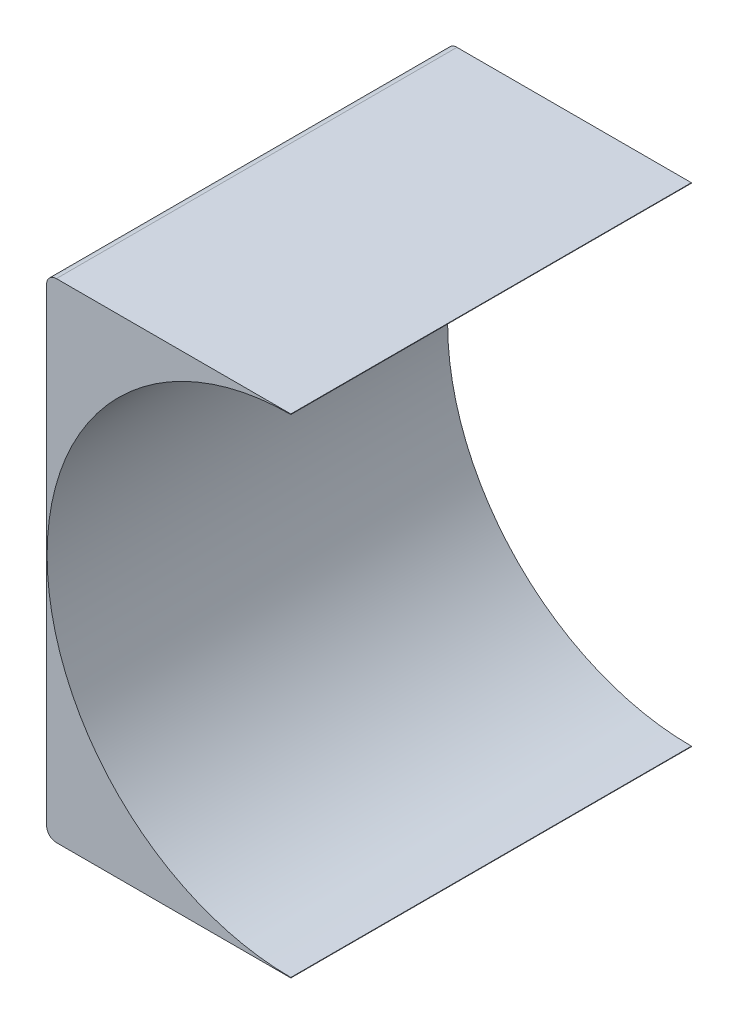
SolidWorks part; units mm, degrees
ref_plane "Спереди" through (0, 0, 0) normal (0, 0, 1) x (1, 0, 0)
ref_plane "Сверху" through (0, 0, 0) normal (0, 1, 0) x (1, 0, 0)
ref_plane "Справа" through (0, 0, 0) normal (1, 0, 0) x (0, 0, -1)
other "Configuration Table"
sketch "Эскиз1" plane through (0, 0, 0) normal (0, 1, 0) x (1, 0, 0)
  line L1 (12.5, -20.5) -> (-12.5, -20.5)
  line L2 (12.5, -20.5) -> (12.5, 20.5)
  line L3 (12.5, 20.5) -> (-12.5, 20.5)
  line L4 (-12.5, -20.5) -> (-12.5, 20.5)
  line L5 (12.5, -20.5) -> (-12.5, 20.5) construction
  line L6 (12.5, 20.5) -> (-12.5, -20.5) construction
  point P0 (0, 0)
  dimension "D1" = 41
  dimension "D2" = 25
extrude "Бобышка-Вытянуть1" add sketch "Эскиз1" along normal blind 50
fillet "Скругление1" radius 1 1 edges at (-12.5, 0, 0)
sketch "Эскиз2" plane through (0, 0, 20.5) normal (0, 0, 1) x (1, 0, 0)
  line L0 (12.5, 50) -> (12.5, 0) construction
  circle A0 centre (12.5, 25) radius 24.95
  dimension "D1" = 49.9
extrude "Вырез-Вытянуть3" cut sketch "Эскиз2" against normal blind 41
fillet "Скругление2" radius 1 1 edges at (-12.5, 50, 0)
